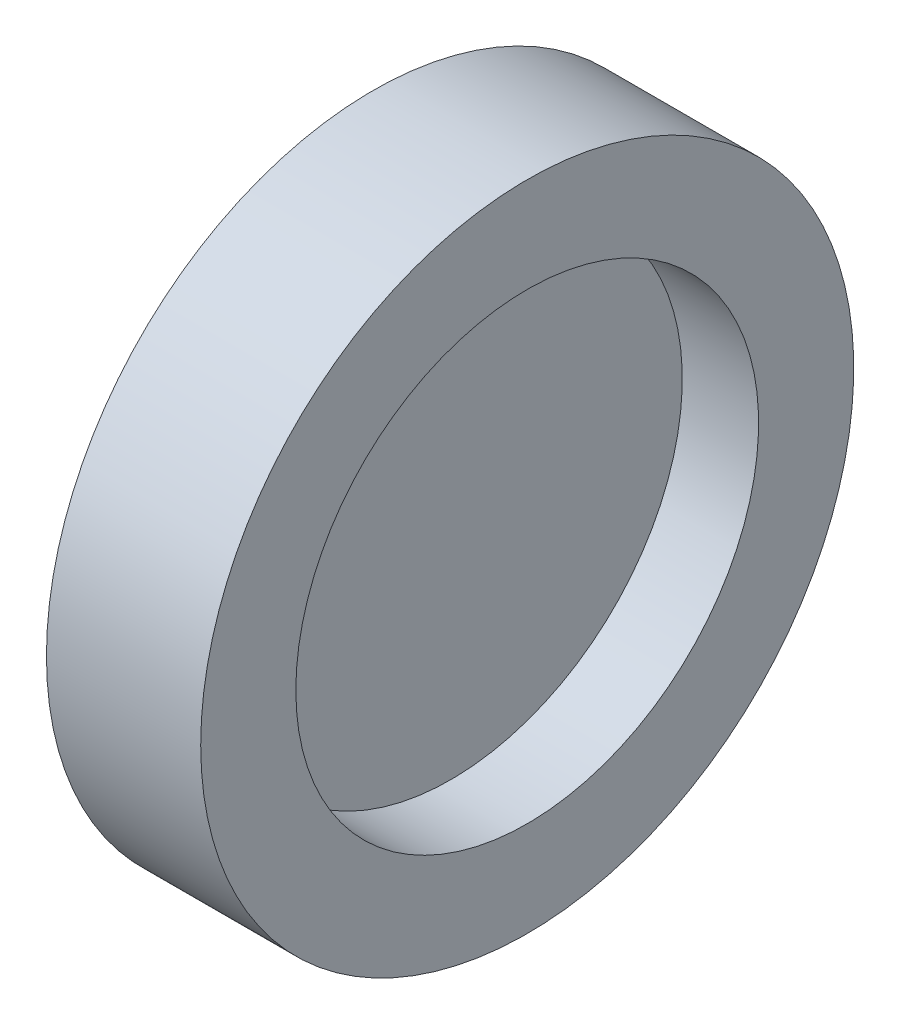
SolidWorks part; units mm, degrees
ref_plane "前视基准面" through (0, 0, 0) normal (0, 0, 1) x (1, 0, 0)
ref_plane "上视基准面" through (0, 0, 0) normal (0, 1, 0) x (1, 0, 0)
ref_plane "右视基准面" through (0, 0, 0) normal (1, 0, 0) x (0, 0, -1)
sketch "草图1" plane through (0, 0, 0) normal (0, 0, 1) x (1, 0, 0)
  line L0 (-0.0305, 9) -> (-0.0305, 0)
  line L2 (-0.0305, 9) -> (0.0305, 9)
  line L3 (-0.0305, 0) -> (0.0305, 0)
  line L4 (0.0305, 9) -> (0.0305, 0)
revolve "旋转2" add sketch "草图1" angle 360 about L3
sketch "草图4" plane through (0, 0, 0) normal (0, 0, 1) x (1, 0, 0)
  line L0 (-3, 12.7) -> (3, 12.7)
  line L1 (3, 12.7) -> (3, 9)
  line L2 (3, 9) -> (-3, 9)
  line L3 (0.0305, 9) -> (-0.0305, 9) construction
  line L4 (-3, 9) -> (-3, 12.7)
  line L5 (0, 9) -> (0, 12.7) construction
  line L6 (-1.6142, 0) -> (1.5903, 0) construction
revolve "旋转3" add sketch "草图4" angle 360 about L6
equation "\"D1@草图4\"=\"D1@草图1\""
